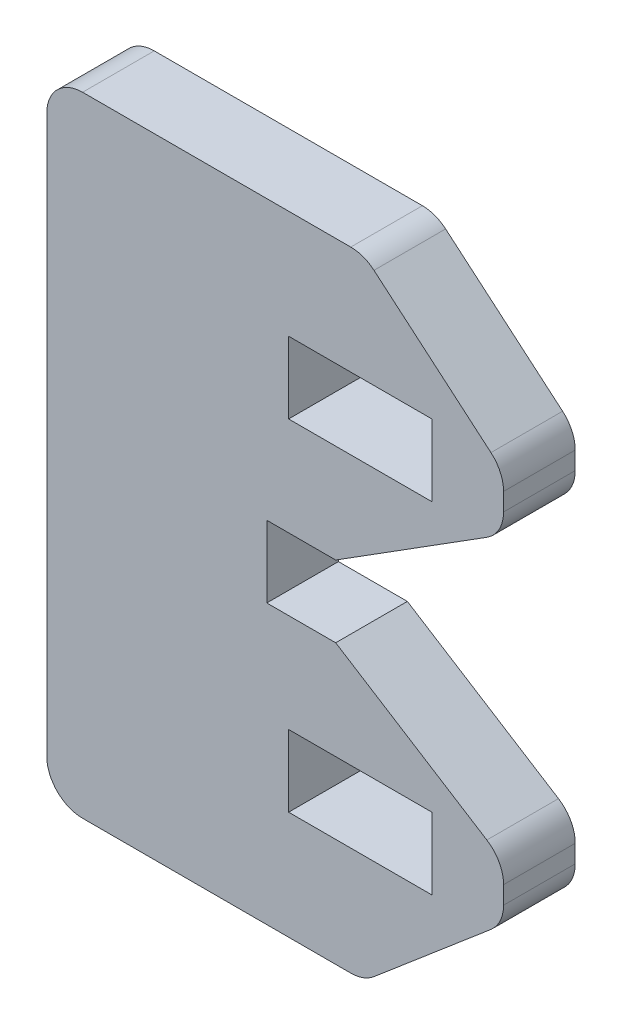
SolidWorks part; units mm, degrees
ref_plane "Front Plane" through (0, 0, 0) normal (0, 0, 1) x (1, 0, 0)
ref_plane "Top Plane" through (0, 0, 0) normal (0, 1, 0) x (1, 0, 0)
ref_plane "Right Plane" through (0, 0, 0) normal (1, 0, 0) x (0, 0, -1)
sketch "Sketch1" plane through (0, 0, 0) normal (0, 0, 1) x (1, 0, 0)
  line L0 (71.634, -1.524) -> (73.1004, -1.524)
  line L1 (66.0194, -1.524) -> (87.6464, -1.524) construction
  line L2 (73.1004, -1.524) -> (76.315, -3.5497)
  line L3 (76.6707, -4.1944) -> (76.6707, -4.5729)
  line L4 (76.4021, -5.1536) -> (73.9141, -7.2675)
  line L5 (73.4207, -7.4488) -> (67.717, -7.4488)
  line L7 (71.634, -1.524) -> (71.634, 0)
  line L8 (75.37, -0.762) -> (73.6227, -0.762) construction
  line L9 (75.37, -1.524) -> (75.37, 0) construction
  line L10 (72.0987, 3.6216) -> (72.0987, 2.0976)
  line L11 (75.1467, -5.1456) -> (72.0987, -5.1456)
  line L12 (75.1467, -5.1456) -> (75.1467, -3.6216)
  line L13 (75.1467, -3.6216) -> (72.0987, -3.6216)
  line L14 (72.0987, -5.1456) -> (72.0987, -3.6216)
  line L15 (75.1467, 2.0976) -> (72.0987, 2.0976)
  line L16 (75.1467, 3.6216) -> (75.1467, 2.0976)
  line L17 (75.1467, 3.6216) -> (72.0987, 3.6216)
  line L18 (66.955, 5.1628) -> (66.955, -6.6868)
  line L19 (73.4207, 5.9248) -> (67.717, 5.9248)
  line L20 (76.4021, 3.6296) -> (73.9141, 5.7435)
  line L21 (76.6707, 2.6704) -> (76.6707, 3.0489)
  line L22 (73.1004, 0) -> (76.315, 2.0257)
  line L23 (73.1004, 0) -> (71.634, 0)
  arc A0 (67.717, -7.4488) -> (66.955, -6.6868) centre (67.717, -6.6868) cw
  arc A1 (73.9141, -7.2675) -> (73.4207, -7.4488) centre (73.4207, -6.6868) cw
  arc A2 (76.6707, -4.5729) -> (76.4021, -5.1536) centre (75.9087, -4.5729) cw
  arc A3 (76.315, -3.5497) -> (76.6707, -4.1944) centre (75.9087, -4.1944) cw
  arc A4 (76.315, 2.0257) -> (76.6707, 2.6704) centre (75.9087, 2.6704) ccw
  arc A5 (76.6707, 3.0489) -> (76.4021, 3.6296) centre (75.9087, 3.0489) ccw
  arc A6 (73.9141, 5.7435) -> (73.4207, 5.9248) centre (73.4207, 5.1628) ccw
  arc A7 (67.717, 5.9248) -> (66.955, 5.1628) centre (67.717, 5.1628) ccw
  dimension "D1" = 0.762
  dimension "D2" = 3.048
  dimension "D3" = 1.524
  dimension "D4" = 1.524
extrude "Boss-Extrude1" add sketch "Sketch1" along normal blind 1.524
